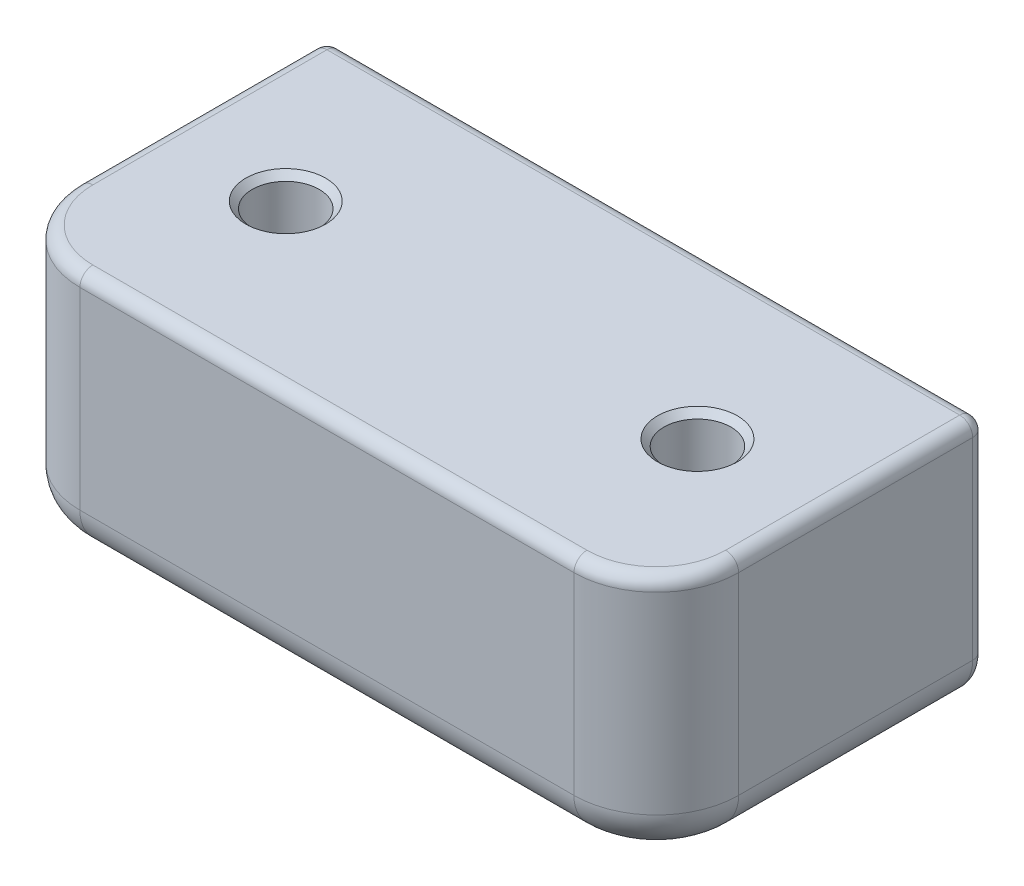
SolidWorks part; units mm, degrees
ref_plane "Front Plane" through (0, 0, 0) normal (0, 0, 1) x (1, 0, 0)
ref_plane "Top Plane" through (0, 0, 0) normal (0, 1, 0) x (1, 0, 0)
ref_plane "Right Plane" through (0, 0, 0) normal (1, 0, 0) x (0, 0, -1)
sketch "Sketch1" plane through (0, 0, 0) normal (0, 1, 0) x (1, 0, 0)
  line L1 (6.35, 0) -> (44.45, 0)
  line L2 (0, 6.35) -> (0, 25.4)
  line L3 (0, 25.4) -> (50.8, 25.4)
  line L4 (50.8, 6.35) -> (50.8, 25.4)
  arc A0 (44.45, 0) -> (50.8, 6.35) centre (44.45, 6.35) ccw
  arc A1 (6.35, 0) -> (0, 6.35) centre (6.35, 6.35) cw
  point P9 (0, 0)
  dimension "D3" = 6.35
  dimension "D1" = 25.4
  dimension "D2" = 50.8
extrude "Boss-Extrude1" add sketch "Sketch1" along normal blind 19.05
sketch "Sketch2" plane through (0, 19.05, 0) normal (0, 1, 0) x (1, 0, 0)
  line L0 (25.4, 31.2839) -> (25.4, -3.6976) construction
  line L1 (50.8, 25.4) -> (0, 25.4) construction
  line L2 (0, 25.4) -> (0, 6.35) construction
  circle A0 centre (9.525, 12.7) radius 2.5797
  circle A1 centre (41.275, 12.7) radius 2.5797
  dimension "D1" = 12.7
  dimension "D2" = 9.525
extrude "Cut-Extrude1" cut sketch "Sketch2" against normal through all
sketch "Sketch3" plane through (0, 0, -25.4) normal (0, 0, -1) x (-1, 0, 0)
  line L0 (-25.4, 23.4198) -> (-25.4, -4.4878) construction
  line L1 (-50.8, 19.05) -> (0, 19.05) construction
  line L2 (-50.8, 19.05) -> (-50.8, 0) construction
  circle A0 centre (-41.275, 9.525) radius 6.604
  circle A1 centre (-9.525, 9.525) radius 6.604
  dimension "D2" = 9.525
  dimension "D1" = 9.525
extrude "Cut-Extrude2" cut sketch "Sketch3" against normal blind 6.604
chamfer "Chamfer1" distance 0.5 angle 45 6 edges at (9.525, 19.05, -10.1203) (9.525, 0, -10.1203) (41.275, 19.05, -15.2797) (41.275, 0, -15.2797) (16.129, 9.525, -25.4) (34.671, 9.525, -25.4)
fillet "Fillet1" radius 3.175 5 edges at (0, 0, -15.875) (1.8599, 0, -1.8599) (25.4, 0, 0) (48.9401, 0, -1.8599) (50.8, 0, -15.875)
fillet "Fillet2" radius 1 11 edges at (50.8, 19.05, -15.875) (48.9401, 19.05, -1.8599) (25.4, 19.05, 0) (1.8599, 19.05, -1.8599) (49.8701, 0.9299, -25.4) (50.8, 11.1125, -25.4) (25.4, 19.05, -25.4) (0, 11.1125, -25.4) (0.9299, 0.9299, -25.4) (25.4, 0, -25.4) (0, 19.05, -15.875)
